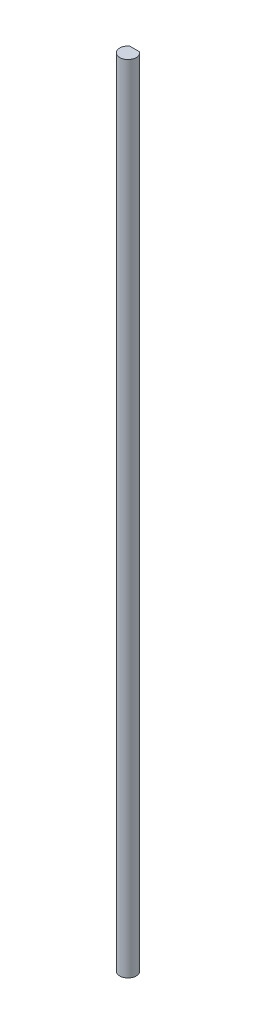
SolidWorks part; units mm, degrees
ref_plane "Front Plane" through (0, 0, 0) normal (0, 0, 1) x (1, 0, 0)
ref_plane "Top Plane" through (0, 0, 0) normal (0, 1, 0) x (1, 0, 0)
ref_plane "Right Plane" through (0, 0, 0) normal (1, 0, 0) x (0, 0, -1)
sketch "Sketch1" plane through (0, 0, 0) normal (0, 1, 0) x (1, 0, 0)
  line L0 (-1.905, 2.54) -> (1.905, 2.54)
  arc A0 (-1.905, 2.54) -> (1.905, 2.54) centre (0, 0) ccw
  dimension "D1" = 6.35
  dimension "D2" = 2.54
extrude "Boss-Extrude1" add sketch "Sketch1" along normal blind 304.8
